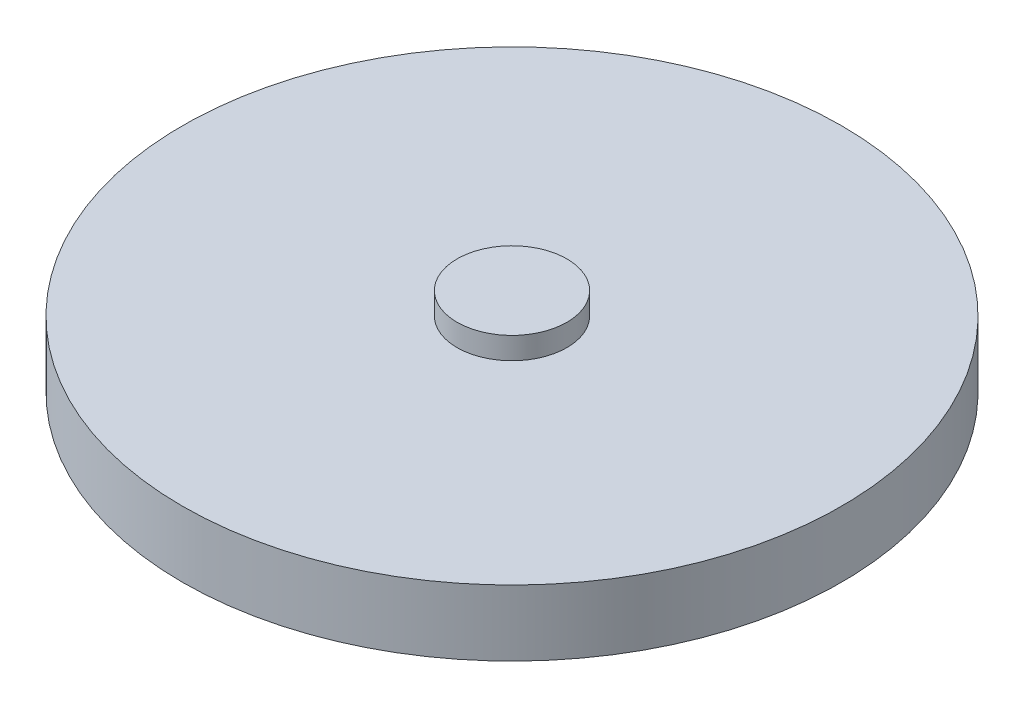
SolidWorks part; units mm, degrees
material "ABS"
ref_plane "Płaszczyzna przednia" through (0, 0, 0) normal (0, 0, 1) x (1, 0, 0)
ref_plane "Płaszczyzna górna" through (0, 0, 0) normal (0, 1, 0) x (1, 0, 0)
ref_plane "Płaszczyzna prawa" through (0, 0, 0) normal (1, 0, 0) x (0, 0, -1)
sketch "Szkic2" plane through (0, 0, 0) normal (0, 1, 0) x (1, 0, 0)
  circle A0 centre (0, 0) radius 150
  dimension "D1" = 300
extrude "Dodanie-wyciągnięcie1" add sketch "Szkic2" along normal blind 30
sketch "Szkic3" plane through (0, 30, 0) normal (0, 1, 0) x (1, 0, 0)
  circle A0 centre (0, 0) radius 25
  dimension "D1" = 50
extrude "Dodanie-wyciągnięcie2" add sketch "Szkic3" along normal blind 10
sketch "Szkic5" plane through (0, 0, 0) normal (0, -1, 0) x (-1, 0, 0)
  circle A0 centre (0, 0) radius 17.5
  dimension "D1" = 35
extrude "Wytnij-wyciągnięcie1" cut sketch "Szkic5" against normal blind 3
